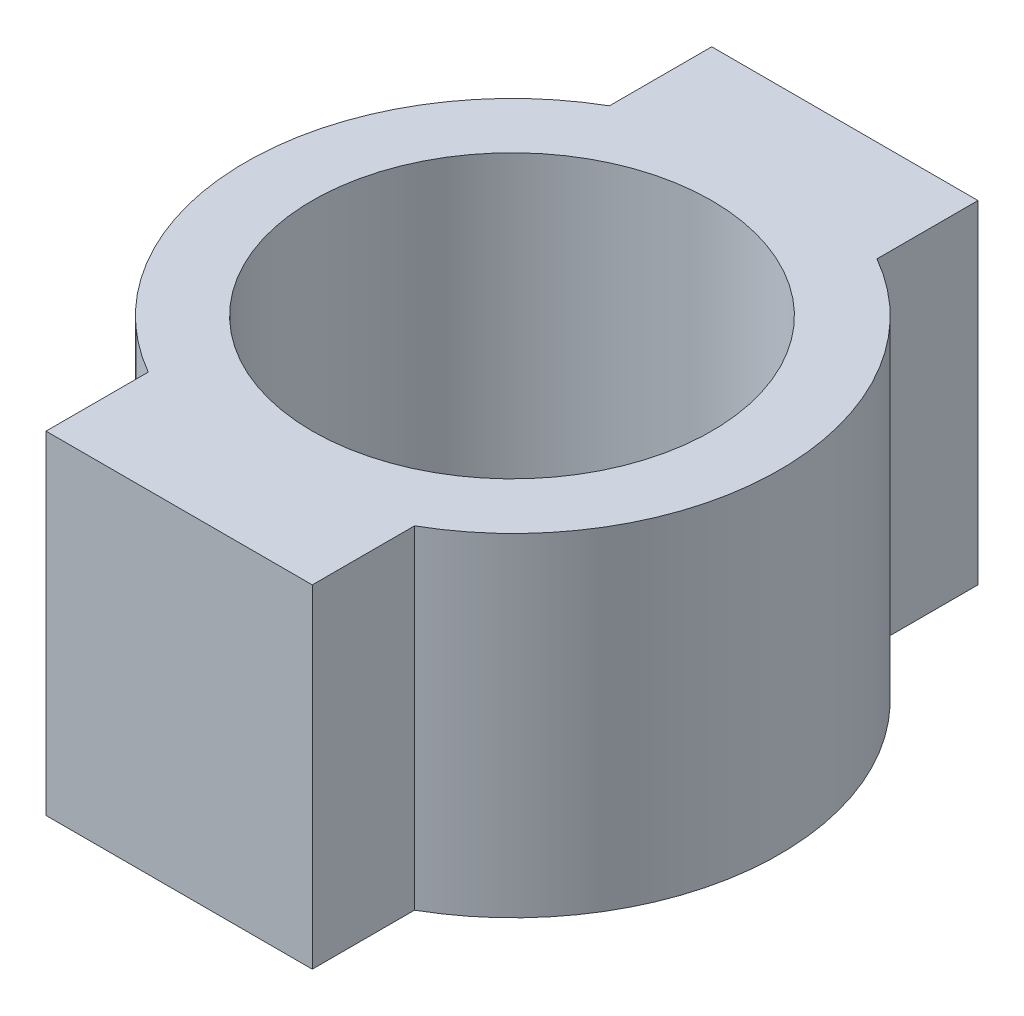
SolidWorks part; units mm, degrees
ref_plane "Front Plane" through (0, 0, 0) normal (0, 0, 1) x (1, 0, 0)
ref_plane "Top Plane" through (0, 0, 0) normal (0, 1, 0) x (1, 0, 0)
ref_plane "Right Plane" through (0, 0, 0) normal (1, 0, 0) x (0, 0, -1)
sketch "Sketch1" plane through (0, 0, 0) normal (0, 1, 0) x (1, 0, 0)
  line L2 (-20, 50) -> (20, 50)
  line L3 (-20, -50) -> (20, -50)
  line L4 (-20, 50) -> (-20, 34.641)
  line L5 (20, 50) -> (20, 34.8186)
  line L6 (20, -50) -> (20, -34.641)
  line L7 (-20, -50) -> (-20, -34.641)
  arc A2 (-20, 34.641) -> (-20, -34.641) centre (0, 0) ccw
  arc A3 (20, 34.8186) -> (20, -34.641) centre (0.1546, 0.0888) cw
  point P1 (-19.9946, -34.641)
  point P10 (0, 50)
  point P13 (0, -50)
  dimension "D7" = 40
  dimension "D4" = 40
  dimension "D5" = 40
extrude "Boss-Extrude1" add sketch "Sketch1" along normal blind 50 contours A3 L6 L3 L7 A2 L4 L2 L5
sketch "Sketch2" plane through (0, 50, 0) normal (0, 1, 0) x (1, 0, 0)
  circle A0 centre (0, 0) radius 30
  dimension "D1" = 60
extrude "Cut-Extrude1" cut sketch "Sketch2" against normal blind 50
